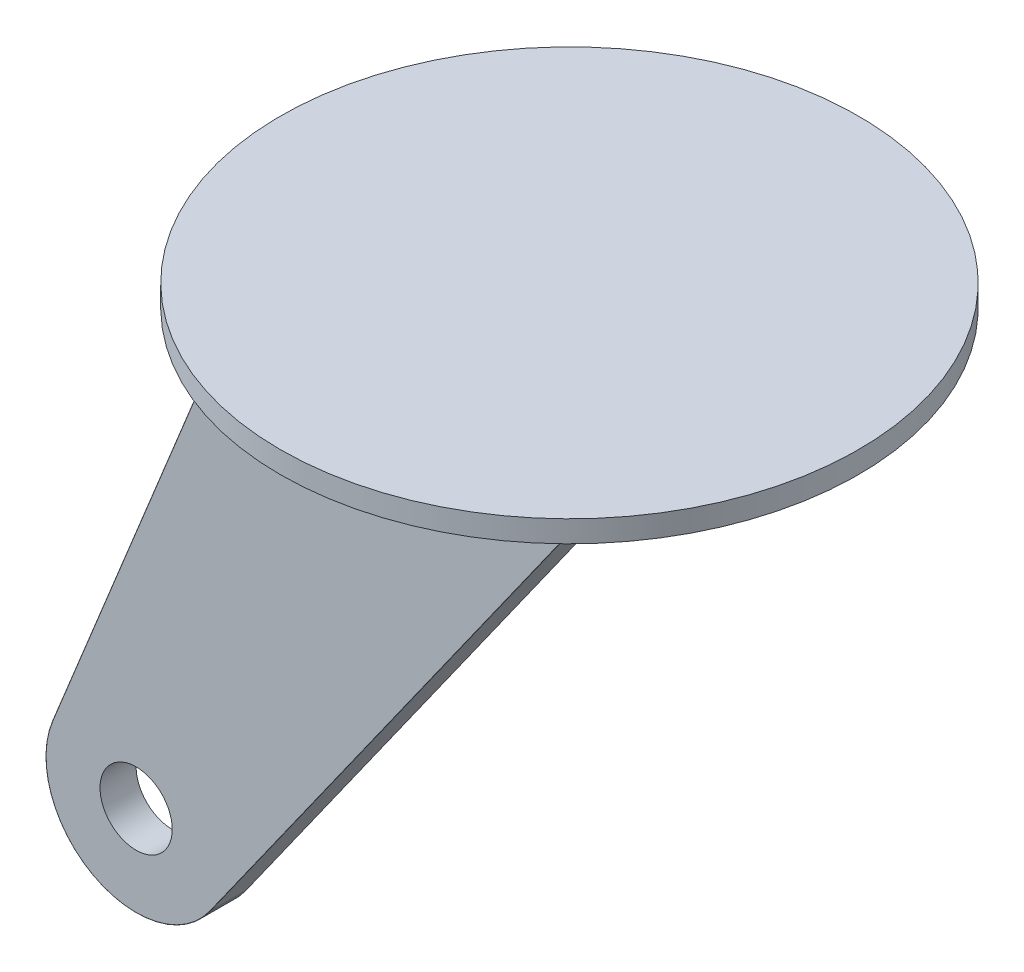
SolidWorks part; units mm, degrees
ref_plane "Front Plane" through (0, 0, 0) normal (0, 0, 1) x (1, 0, 0)
ref_plane "Top Plane" through (0, 0, 0) normal (0, 1, 0) x (1, 0, 0)
ref_plane "Right Plane" through (0, 0, 0) normal (1, 0, 0) x (0, 0, -1)
sketch "Sketch1" plane through (0, 0, 0) normal (0, 1, 0) x (1, 0, 0)
  circle A0 centre (0, 0) radius 1016
  dimension "D1" = 2032
extrude "Boss-Extrude1" add sketch "Sketch1" along normal blind 76.2
ref_plane "Plane1" through (0, 0, 381) normal (0, 0, 1) x (1, 0, 0)
sketch "Sketch2" plane through (0, 0, 381) normal (0, 0, 1) x (1, 0, 0)
  line L0 (0, 0) -> (635, 0)
  line L1 (-1016, 0) -> (1016, 0) construction
  line L2 (0, 0) -> (-635, 0)
  line L3 (-635, 0) -> (-1309.4451, -1658.3901)
  line L4 (635, 0) -> (-756.3636, -1961.6821)
  arc A0 (-1309.4451, -1658.3901) -> (-756.3636, -1961.6821) centre (-1015.3368, -1778) ccw
  circle A1 centre (-1015.3368, -1778) radius 127
  dimension "D3" = 635
  dimension "D5" = 254
  dimension "D1" = 635
  dimension "D2" = 635
  dimension "D4" = 1778
extrude "Boss-Extrude3" add sketch "Sketch2" along normal blind 127
fillet "Fillet1" radius 1 6 edges at (-60.6818, -980.8411, 381) (-60.6818, -980.8411, 508) (-1167.997, -2056.3902, 508) (-1167.997, -2056.3902, 381) (-972.2226, -829.195, 381) (-972.2226, -829.195, 508)
